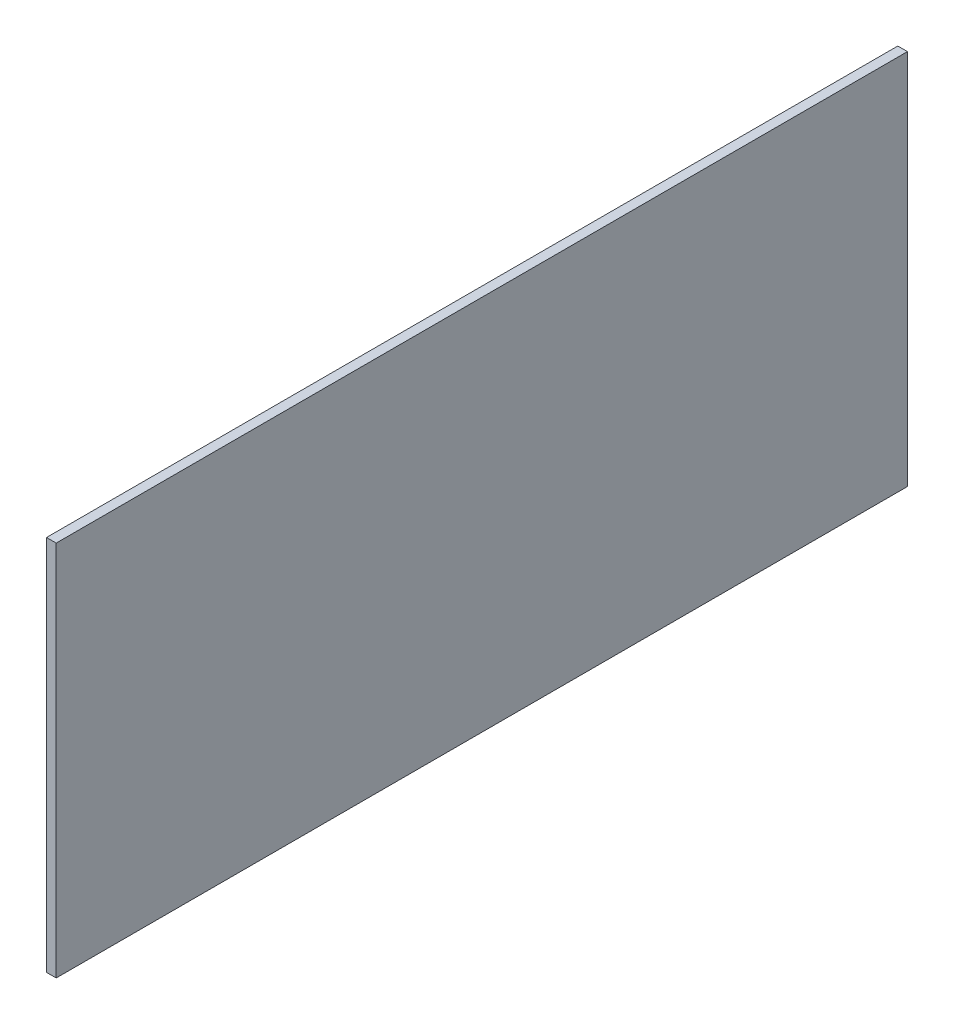
SolidWorks part; units mm, degrees
ref_plane "Спереди" through (0, 0, 0) normal (0, 0, 1) x (1, 0, 0)
ref_plane "Сверху" through (0, 0, 0) normal (0, 1, 0) x (1, 0, 0)
ref_plane "Справа" through (0, 0, 0) normal (1, 0, 0) x (0, 0, -1)
sketch "Эскиз1" plane through (0, 0, 0) normal (1, 0, 0) x (0, 0, -1)
  line L0 (1311.8915, 409.3492) -> (1311.8915, -290.6508)
  line L1 (1311.8915, -290.6508) -> (-270.1085, -290.6508)
  line L6 (-270.1085, -290.6508) -> (-270.1085, 409.3492)
  line L7 (-270.1085, 409.3492) -> (1311.8915, 409.3492)
  dimension "D1" = 1582
  dimension "D2" = 700
extrude "Бобышка-Вытянуть1" add sketch "Эскиз1" along normal blind 18
